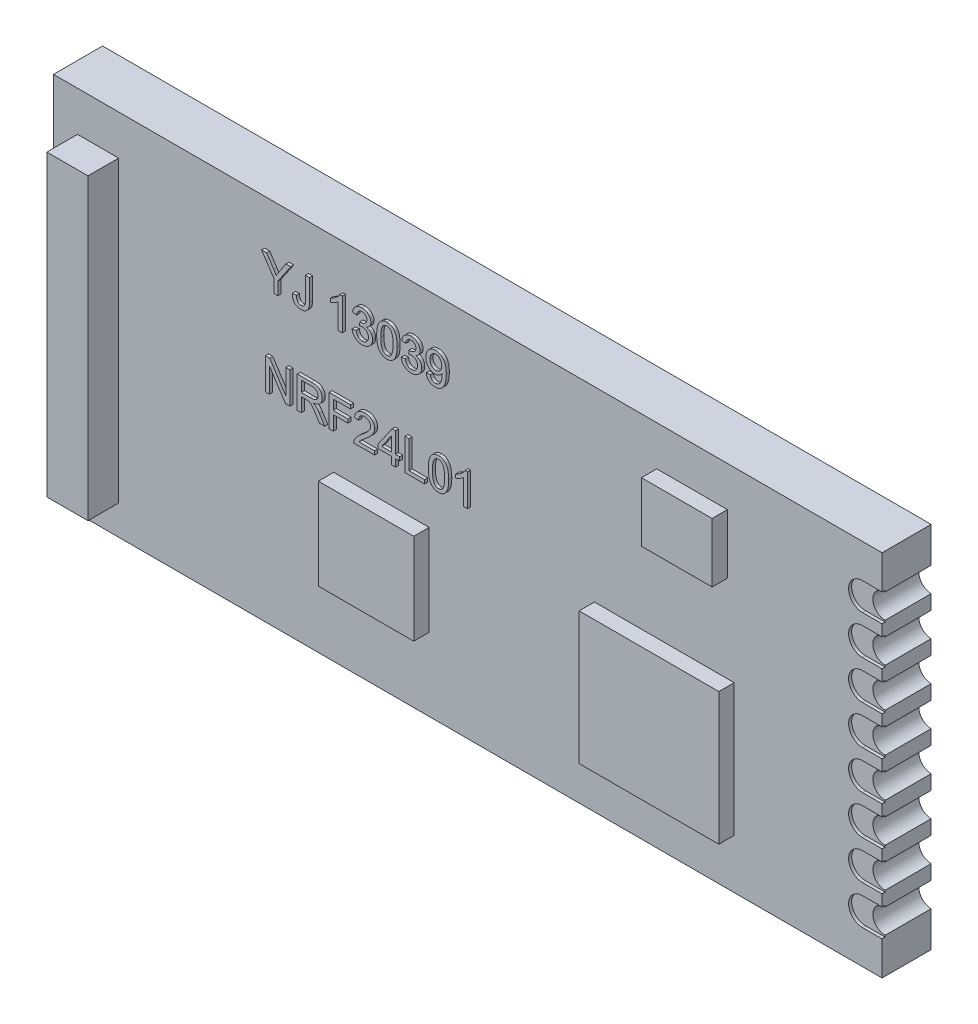
SolidWorks part; units mm, degrees
ref_plane "Plan de face" through (0, 0, 0) normal (0, 0, 1) x (1, 0, 0)
ref_plane "Plan de dessus" through (0, 0, 0) normal (0, 1, 0) x (1, 0, 0)
ref_plane "Plan de droite" through (0, 0, 0) normal (1, 0, 0) x (0, 0, -1)
sketch "Esquisse1" plane through (0, 0, 0) normal (0, 0, 1) x (1, 0, 0)
  line L1 (0, 0) -> (27, 0)
  line L2 (0, 0) -> (0, 12)
  line L3 (0, 12) -> (27, 12)
  line L4 (27, 0) -> (27, 12)
  dimension "D1" = 27
  dimension "D2" = 12
extrude "Boss.-Extru.1" add sketch "Esquisse1" along normal blind 1.6
sketch "Esquisse3" plane through (0, 0, 1.6) normal (0, 0, 1) x (1, 0, 0)
  line L0 (27, 6) -> (27, 6.635) construction
  line L1 (27, 0) -> (27, 12) construction
  line L2 (27, 6) -> (30.5028, 6) construction
  circle A0 centre (27, 6.635) radius 0.4
  circle A1 centre (27, 7.905) radius 0.4
  circle A2 centre (27, 9.175) radius 0.4
  circle A3 centre (27, 10.445) radius 0.4
  circle A4 centre (27, 1.555) radius 0.4
  circle A5 centre (27, 2.825) radius 0.4
  circle A6 centre (27, 4.095) radius 0.4
  circle A7 centre (27, 5.365) radius 0.4
  dimension "D2" = 4
  dimension "D1" = 0.635
extrude "Enlèv. mat.-Extru.1" cut sketch "Esquisse3" against normal blind 1.6
sketch "Esquisse4" plane through (0, 0, 1.6) normal (0, 0, 1) x (1, 0, 0)
  line L0 (27, 9.9948) -> (26.359, 9.9948)
  line L2 (27, 9.575) -> (27, 10.045) construction
  line L3 (26.359, 9.6247) -> (27, 9.6247)
  line L4 (26.359, 10.8947) -> (27, 10.8947)
  line L5 (27, 10.845) -> (27, 12) construction
  line L6 (27, 9.575) -> (27, 9.6247)
  line L7 (27, 8.775) -> (27, 8.7248)
  line L8 (27, 8.7248) -> (26.359, 8.7248)
  line L9 (26.359, 8.3547) -> (27, 8.3547)
  line L10 (27, 8.305) -> (27, 8.3547)
  line L11 (27, 7.505) -> (27, 7.4548)
  line L12 (27, 7.4548) -> (26.359, 7.4548)
  line L13 (26.359, 7.0847) -> (27, 7.0847)
  line L14 (27, 7.035) -> (27, 7.0847)
  line L15 (27, 6.235) -> (27, 6.1848)
  line L16 (27, 6.1848) -> (26.359, 6.1848)
  line L17 (26.359, 5.8147) -> (27, 5.8147)
  line L18 (27, 5.765) -> (27, 5.8147)
  line L19 (27, 10.845) -> (27, 10.8947)
  line L20 (27, 10.045) -> (27, 9.9948)
  line L21 (27, 4.965) -> (27, 4.9148)
  line L22 (27, 4.9148) -> (26.359, 4.9148)
  line L23 (26.359, 4.5447) -> (27, 4.5447)
  line L24 (27, 4.495) -> (27, 4.5447)
  line L25 (27, 3.695) -> (27, 3.6448)
  line L26 (27, 3.6448) -> (26.359, 3.6448)
  line L27 (26.359, 3.2747) -> (27, 3.2747)
  line L28 (27, 3.225) -> (27, 3.2747)
  line L29 (27, 2.425) -> (27, 2.3748)
  line L30 (27, 2.3748) -> (26.359, 2.3748)
  line L31 (26.359, 2.0047) -> (27, 2.0047)
  line L32 (27, 1.955) -> (27, 2.0047)
  line L33 (27, 1.155) -> (27, 1.1048)
  line L34 (27, 1.1048) -> (26.359, 1.1048)
  arc A0 (27, 10.845) -> (27, 10.045) centre (27, 10.445) ccw
  arc A1 (26.359, 10.8947) -> (26.359, 9.9948) centre (26.359, 10.4448) ccw
  arc A2 (27, 9.575) -> (27, 8.775) centre (27, 9.175) ccw
  arc A3 (26.359, 9.6247) -> (26.359, 8.7248) centre (26.359, 9.1748) ccw
  arc A4 (27, 8.305) -> (27, 7.505) centre (27, 7.905) ccw
  arc A5 (26.359, 8.3547) -> (26.359, 7.4548) centre (26.359, 7.9048) ccw
  arc A6 (27, 7.035) -> (27, 6.235) centre (27, 6.635) ccw
  arc A7 (26.359, 7.0847) -> (26.359, 6.1848) centre (26.359, 6.6348) ccw
  arc A8 (27, 5.765) -> (27, 4.965) centre (27, 5.365) ccw
  arc A9 (26.359, 5.8147) -> (26.359, 4.9148) centre (26.359, 5.3648) ccw
  arc A10 (27, 4.495) -> (27, 3.695) centre (27, 4.095) ccw
  arc A11 (26.359, 4.5447) -> (26.359, 3.6448) centre (26.359, 4.0948) ccw
  arc A12 (27, 3.225) -> (27, 2.425) centre (27, 2.825) ccw
  arc A13 (26.359, 3.2747) -> (26.359, 2.3748) centre (26.359, 2.8248) ccw
  arc A14 (27, 1.955) -> (27, 1.155) centre (27, 1.555) ccw
  arc A15 (26.359, 2.0047) -> (26.359, 1.1048) centre (26.359, 1.5548) ccw
  dimension "D1" = 8
extrude "Enlèv. mat.-Extru.2" cut sketch "Esquisse4" against normal blind 0.1
sketch "Esquisse5" plane through (0, 0, 1.6) normal (0, 0, 1) x (1, 0, 0)
  line L1 (0.784, 10.6987) -> (2.1242, 10.6987)
  line L2 (0.784, 10.6987) -> (0.784, 0.9662)
  line L3 (0.784, 0.9662) -> (2.1242, 0.9662)
  line L4 (2.1242, 10.6987) -> (2.1242, 0.9662)
extrude "Boss.-Extru.2" add sketch "Esquisse5" along normal blind 1
sketch "Esquisse6" plane through (0, 0, 1.6) normal (0, 0, 1) x (1, 0, 0)
  line L1 (22.1809, 1.6154) -> (17.6275, 1.6154)
  line L2 (22.1809, 1.6154) -> (22.1809, 5.924)
  line L3 (22.1809, 5.924) -> (17.6275, 5.924)
  line L4 (17.6275, 1.6154) -> (17.6275, 5.924)
extrude "Boss.-Extru.3" add sketch "Esquisse6" along normal blind 0.5
sketch "Esquisse7" plane through (0, 0, 1.6) normal (0, 0, 1) x (1, 0, 0)
  line L1 (19.6594, 8.7638) -> (21.9606, 8.7638)
  line L2 (19.6594, 8.7638) -> (19.6594, 10.6978)
  line L3 (19.6594, 10.6978) -> (21.9606, 10.6978)
  line L4 (21.9606, 8.7638) -> (21.9606, 10.6978)
extrude "Boss.-Extru.4" add sketch "Esquisse7" along normal blind 0.5
sketch "Esquisse8" plane through (0, 0, 1.6) normal (0, 0, 1) x (1, 0, 0)
  line L1 (9.1326, 2.3743) -> (12.2417, 2.3743)
  line L2 (9.1326, 2.3743) -> (9.1326, 5.3365)
  line L3 (9.1326, 5.3365) -> (12.2417, 5.3365)
  line L4 (12.2417, 2.3743) -> (12.2417, 5.3365)
extrude "Boss.-Extru.5" add sketch "Esquisse8" along normal blind 0.5
sketch "Esquisse9" plane through (0, 0, 1.6) normal (0, 0, 1) x (1, 0, 0)
  text T0 "YJ 13039\r\nNRF24L01" font "@Arial Unicode MS" height in points 4
extrude "Boss.-Extru.6" add sketch "Esquisse9" along normal blind 0.1
